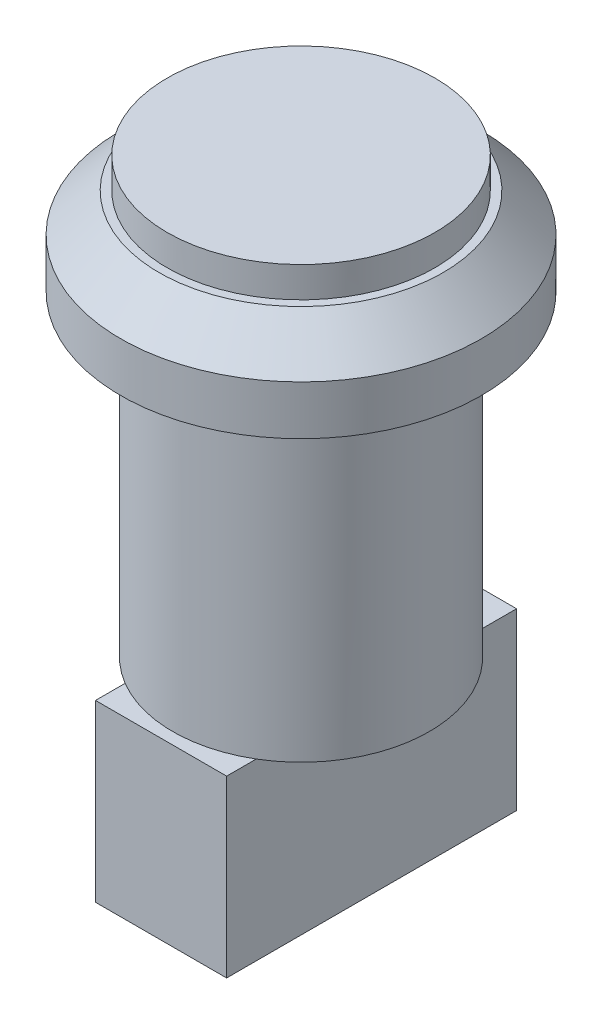
SolidWorks part; units mm, degrees
ref_plane "Front Plane" through (0, 0, 0) normal (0, 0, 1) x (1, 0, 0)
ref_plane "Top Plane" through (0, 0, 0) normal (0, 1, 0) x (1, 0, 0)
ref_plane "Right Plane" through (0, 0, 0) normal (1, 0, 0) x (0, 0, -1)
sketch "Sketch1" plane through (0, 0, 0) normal (0, 1, 0) x (1, 0, 0)
  circle A0 centre (0, 0) radius 12.25
  dimension "D1" = 24.5
extrude "Boss-Extrude1" add sketch "Sketch1" along normal blind 2.8
sketch "Sketch2" plane through (0, 0, 0) normal (0, -1, 0) x (1, 0, 0)
  circle A0 centre (0, 0) radius 16.5
  dimension "D1" = 33
extrude "Boss-Extrude2" add sketch "Sketch2" along normal blind 8
chamfer "Chamfer1" distance 3.5 angle 45 1 edges at (0, 0, -16.5)
sketch "Sketch3" plane through (0, -8, 0) normal (0, -1, 0) x (1, 0, 0)
  circle A0 centre (0, 0) radius 11.75
  dimension "D1" = 23.5
extrude "Boss-Extrude3" add sketch "Sketch3" along normal blind 29
sketch "Sketch4" plane through (0, -37, 0) normal (0, -1, 0) x (1, 0, 0)
  line L0 (0, 16.5) -> (0, -16.5) construction
  line L2 (-6, 12.8118) -> (6, 12.8118)
  line L3 (-6, 12.8118) -> (-6, -13.7221)
  line L4 (-6, -13.7221) -> (6, -13.7221)
  line L5 (6, 12.8118) -> (6, -13.7221)
  circle A0 centre (0, 0) radius 16.5 construction
  point P9 (0, 12.8118)
  dimension "D1" = 12
extrude "Boss-Extrude4" add sketch "Sketch4" along normal blind 16
